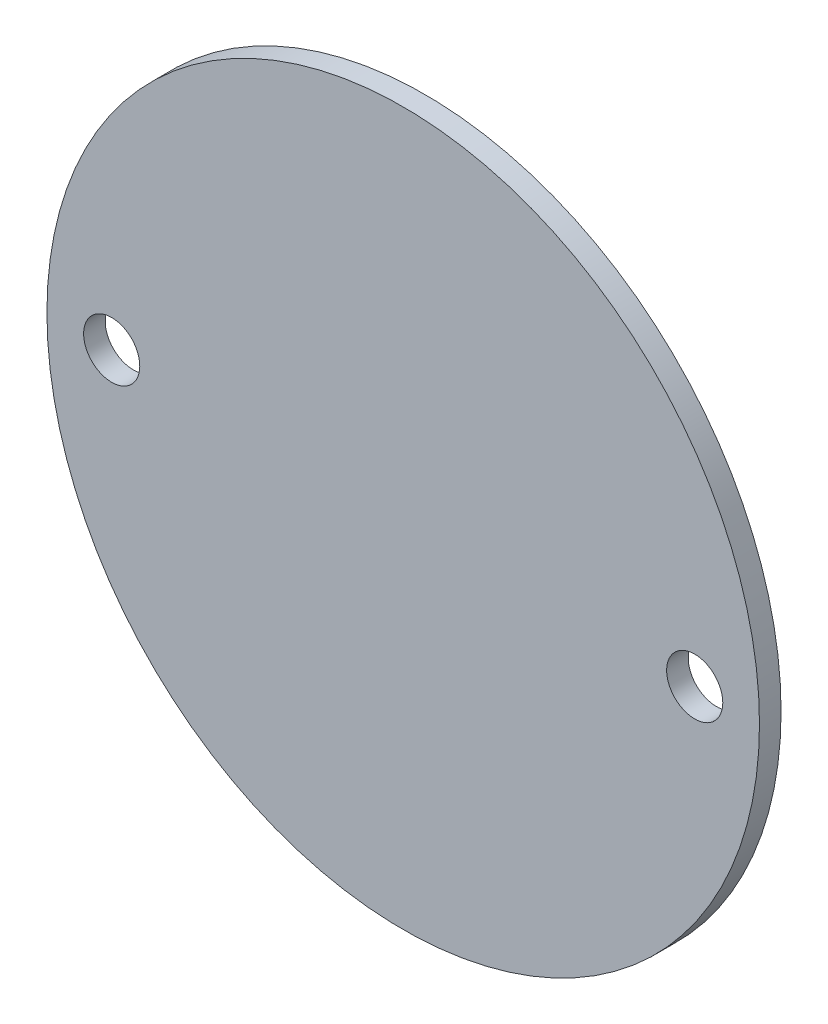
SolidWorks part; units mm, degrees
ref_plane "Front" through (0, 0, 0) normal (0, 0, 1) x (1, 0, 0)
ref_plane "Top" through (0, 0, 0) normal (0, 1, 0) x (1, 0, 0)
ref_plane "Right" through (0, 0, 0) normal (1, 0, 0) x (0, 0, -1)
sketch "草图1" plane through (0, 0, 0) normal (0, 0, 1) x (1, 0, 0)
  circle A0 centre (0, 0) radius 33
  circle A1 centre (27, 0) radius 2.6
  circle A2 centre (-27, 0) radius 2.6
  dimension "D1" = 27
  dimension "D2" = 27
extrude "凸台-拉伸1" add sketch "草图1" along normal blind 2
